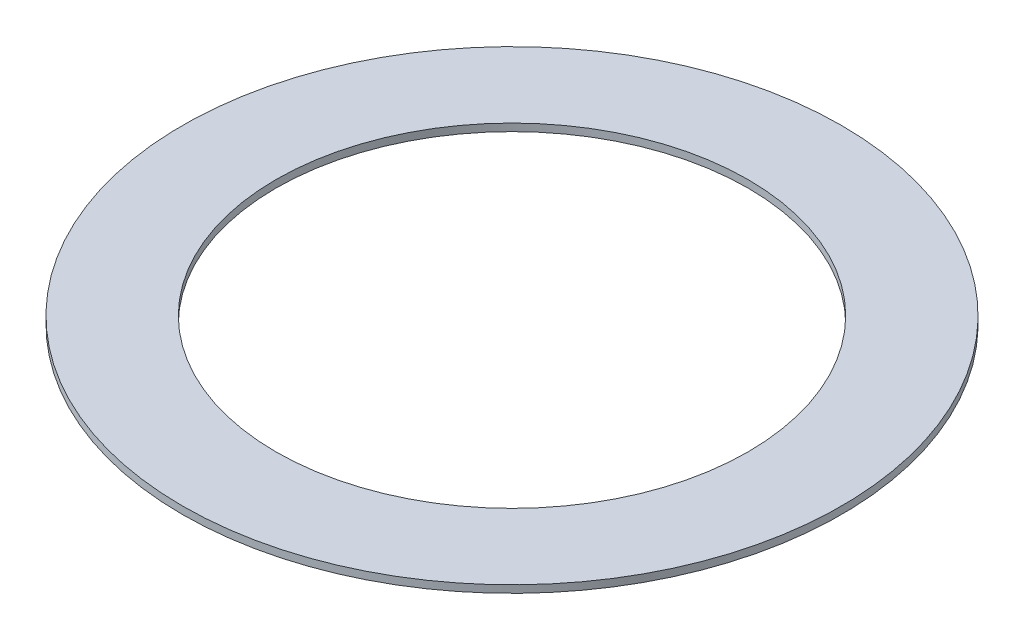
SolidWorks part; units mm, degrees
material "Oak"
ref_plane "Front Plane" through (0, 0, 0) normal (0, 0, 1) x (1, 0, 0)
ref_plane "Top Plane" through (0, 0, 0) normal (0, 1, 0) x (1, 0, 0)
ref_plane "Right Plane" through (0, 0, 0) normal (1, 0, 0) x (0, 0, -1)
sketch "Sketch1" plane through (0, 0, 0) normal (0, 1, 0) x (1, 0, 0)
  circle A0 centre (0, 0) radius 76.2
  circle A1 centre (0, 0) radius 106.426
  dimension "D1" = 152.4
  dimension "D2" = 212.852
extrude "Boss-Extrude1" add sketch "Sketch1" along normal blind 2.4
